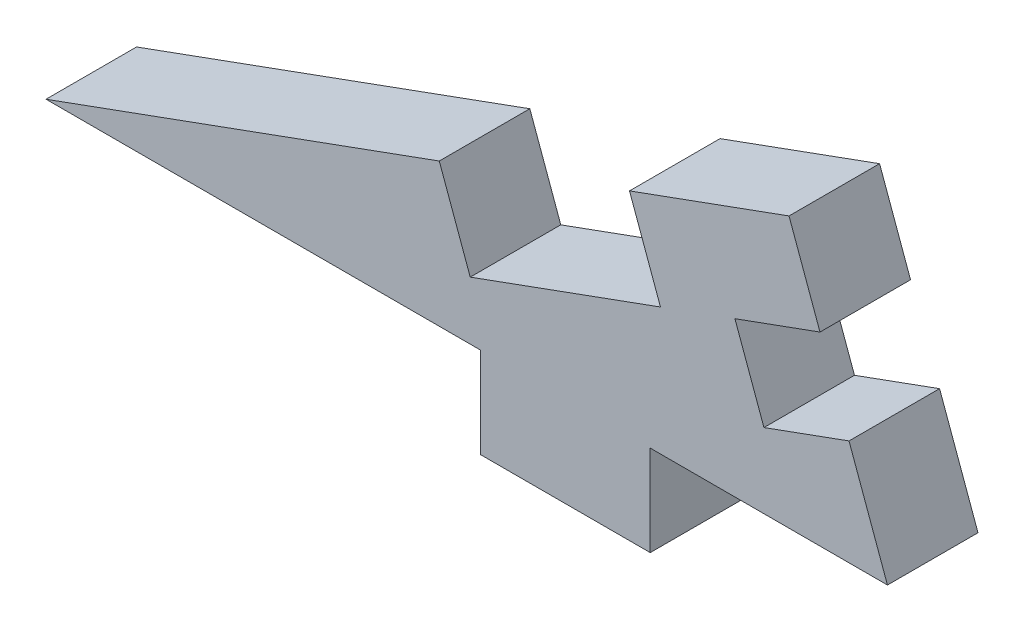
SolidWorks part; units mm, degrees
ref_plane "Front Plane" through (0, 0, 0) normal (0, 0, 1) x (1, 0, 0)
ref_plane "Top Plane" through (0, 0, 0) normal (0, 1, 0) x (1, 0, 0)
ref_plane "Right Plane" through (0, 0, 0) normal (1, 0, 0) x (0, 0, -1)
sketch "Sketch1" plane through (0, 0, 0) normal (0, 0, 1) x (1, 0, 0)
  line L0 (8.9506, 3.2577) -> (19.6244, 7.1427)
  line L1 (28.575, 10.4004) -> (28.575, 0)
  line L3 (0, 0) -> (-1.7375, 4.7736)
  line L4 (9.525, 0) -> (19.05, 0)
  line L5 (9.525, 0) -> (9.525, -5.08)
  line L6 (9.525, -5.08) -> (19.05, -5.08)
  line L7 (19.05, 0) -> (19.05, -5.08)
  line L8 (-1.7375, 4.7736) -> (7.2131, 8.0314)
  line L9 (7.2131, 8.0314) -> (8.9506, 3.2577)
  line L10 (28.575, 10.4004) -> (26.8375, 15.1741)
  line L12 (17.887, 11.9163) -> (19.6244, 7.1427)
  line L15 (26.8375, 15.1741) -> (17.887, 11.9163)
  line L17 (0, 0) -> (9.525, 0)
  line L18 (19.05, 0) -> (28.575, 0)
  dimension "D1" = 20
  dimension "D2" = 28.575
  dimension "D3" = 9.525
  dimension "D4" = 5.08
  dimension "D5" = 5.08
  dimension "D6" = 9.525
extrude "Boss-Extrude1" add sketch "Sketch1" along normal blind 5.08
sketch "Sketch2" plane through (0, 0, 5.08) normal (0, 0, 1) x (1, 0, 0)
  line L0 (28.575, 10.4004) -> (28.575, 0)
  line L1 (28.575, 0) -> (32.3605, 0)
  line L2 (32.3605, 0) -> (28.575, 10.4004)
  line L3 (28.575, 10.4004) -> (26.8375, 15.1741) construction
  line L4 (0, 0) -> (-14.8529, 0)
  line L5 (-14.8529, 0) -> (-1.7375, 4.7736)
  line L6 (-1.7375, 4.7736) -> (0, 0)
  line L7 (-1.7375, 4.7736) -> (7.2131, 8.0314) construction
extrude "Boss-Extrude2" add sketch "Sketch2" against normal up to surface (5.08 mm away) up to face at (14.8519, 3.8874, 0)
sketch "Sketch3" plane through (0, 0, 5.08) normal (0, 0, 1) x (1, 0, 0)
  line L0 (28.575, 10.4004) -> (30.2039, 5.9252)
  line L1 (28.575, 10.4004) -> (23.8014, 8.663)
  line L2 (30.2039, 5.9252) -> (25.4302, 4.1877)
  line L3 (23.8014, 8.663) -> (25.4302, 4.1877)
  line L4 (32.3605, 0) -> (26.8375, 15.1741) construction
  line L5 (8.9506, 3.2577) -> (19.6244, 7.1427) construction
  dimension "D1" = 5.08
  dimension "D2" = 4.7625
extrude "Cut-Extrude1" cut sketch "Sketch3" against normal through all
